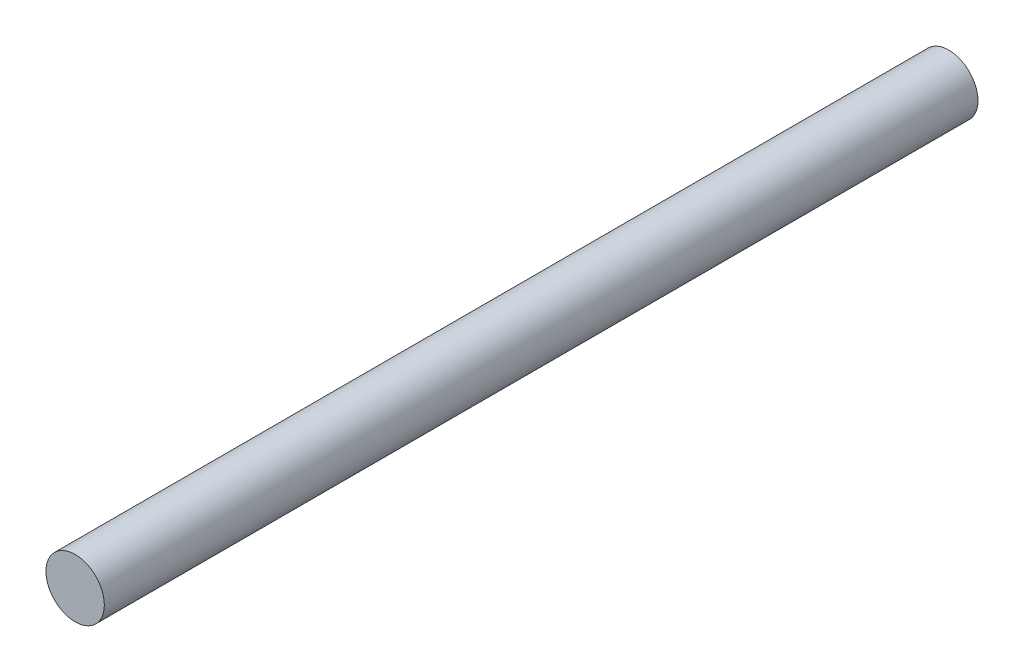
SolidWorks part; units mm, degrees
ref_plane "Front Plane" through (0, 0, 0) normal (0, 0, 1) x (1, 0, 0)
ref_plane "Top Plane" through (0, 0, 0) normal (0, 1, 0) x (1, 0, 0)
ref_plane "Right Plane" through (0, 0, 0) normal (1, 0, 0) x (0, 0, -1)
sketch "Sketch1" plane through (0, 0, 0) normal (0, 0, 1) x (1, 0, 0)
  circle A0 centre (0, 0) radius 3.175
  dimension "D1" = 6.35
extrude "Boss-Extrude1" add sketch "Sketch1" along normal mid plane 95
